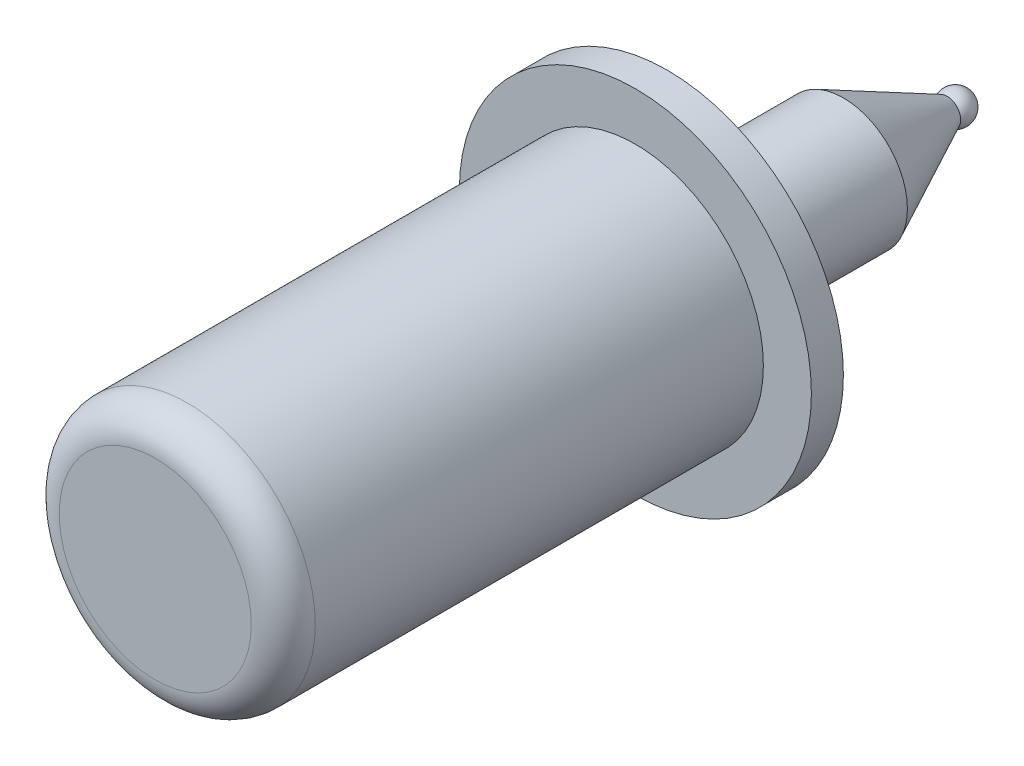
SolidWorks part; units mm, degrees
ref_plane "Front" through (0, 0, 0) normal (0, 0, 1) x (1, 0, 0)
ref_plane "Top" through (0, 0, 0) normal (0, 1, 0) x (1, 0, 0)
ref_plane "Right" through (0, 0, 0) normal (1, 0, 0) x (0, 0, -1)
sketch "Sketch5" plane through (0, 0, 0) normal (1, 0, 0) x (0, 0, -1)
  line L0 (0, 0) -> (-6.5516, 0) construction
  line L1 (0, 0) -> (0, 3)
  line L2 (1, 4) -> (15, 4)
  line L3 (16, 5.5) -> (16, 2)
  line L4 (16, 2) -> (21.5, 2)
  line L5 (15, 4) -> (15, 5.5)
  line L6 (15, 5.5) -> (16, 5.5)
  line L7 (0, 0) -> (34.3456, 0) construction
  line L8 (25.5, 0) -> (0, 0)
  line L9 (24.739, 0.4265) -> (21.5, 2)
  arc A1 (25.5, 0) -> (24.739, 0.4265) centre (25, 0) ccw
  arc A4 (0, 3) -> (1, 4) centre (1, 3) cw
  point P21 (0, 4)
  dimension "D4" = 4
  dimension "D8" = 0.5
  dimension "D9" = 11
  dimension "D7" = 1
  dimension "D1" = 8
  dimension "D2" = 16
  dimension "D3" = 25
  dimension "D5" = 4
  dimension "D10" = 1
revolve "Revolve1" add sketch "Sketch5" angle 360 about L7
